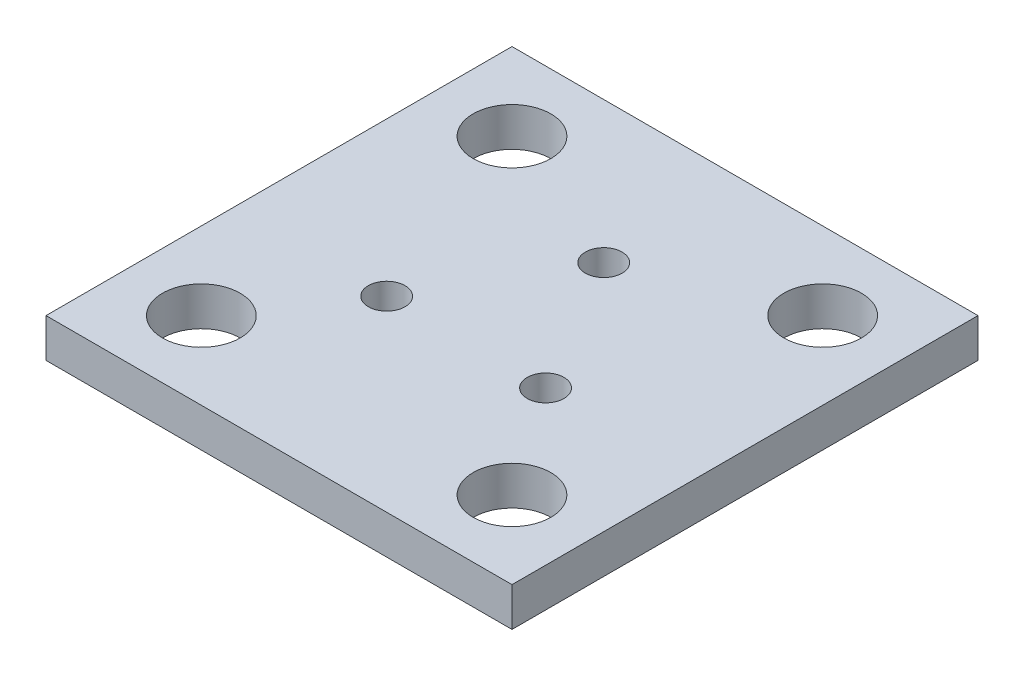
SolidWorks part; units mm, degrees
ref_plane "Front Plane" through (0, 0, 0) normal (0, 0, 1) x (1, 0, 0)
ref_plane "Top Plane" through (0, 0, 0) normal (0, 1, 0) x (1, 0, 0)
ref_plane "Right Plane" through (0, 0, 0) normal (1, 0, 0) x (0, 0, -1)
sketch "Sketch1" plane through (0, 0, 0) normal (0, 1, 0) x (1, 0, 0)
  line L1 (-19.05, -19.05) -> (19.05, -19.05)
  line L2 (-19.05, -19.05) -> (-19.05, 19.05)
  line L3 (-19.05, 19.05) -> (19.05, 19.05)
  line L4 (19.05, -19.05) -> (19.05, 19.05)
  line L5 (-19.05, -19.05) -> (19.05, 19.05) construction
  line L6 (-19.05, 19.05) -> (19.05, -19.05) construction
  circle A0 centre (0, 0) radius 19.05 construction
  dimension "D1" = 38.1
  dimension "D2" = 38.1
  dimension "D3" = 38.1
extrude "Boss-Extrude1" add sketch "Sketch1" along normal blind 3.175
sketch "Sketch2" plane through (0, 3.175, 0) normal (0, 1, 0) x (1, 0, 0)
  circle A0 centre (0, 0) radius 7.5 construction
  circle A1 centre (0, 7.5) radius 1.5
  circle A2 centre (6.4952, -3.75) radius 1.5
  circle A3 centre (-6.4952, -3.75) radius 1.5
  point P11 (0, 0)
  dimension "D2" = 15
  dimension "D3" = 3
  dimension "D1" = 3
extrude "Cut-Extrude1" cut sketch "Sketch2" against normal through all contours A1 | A3 | A2
sketch "Sketch3" plane through (0, 3.175, 0) normal (0, 1, 0) x (1, 0, 0)
  line L1 (-12.7, -12.7) -> (12.7, -12.7) construction
  line L2 (-12.7, -12.7) -> (-12.7, 12.7) construction
  line L3 (-12.7, 12.7) -> (12.7, 12.7) construction
  line L4 (12.7, -12.7) -> (12.7, 12.7) construction
  line L5 (-12.7, -12.7) -> (12.7, 12.7) construction
  line L6 (-12.7, 12.7) -> (12.7, -12.7) construction
  circle A0 centre (-12.7, 12.7) radius 3.175
  circle A1 centre (12.7, 12.7) radius 3.175
  circle A2 centre (12.7, -12.7) radius 3.175
  circle A3 centre (-12.7, -12.7) radius 3.175
  point P0 (0, 0)
  dimension "D3" = 6.35
  dimension "D1" = 25.4
  dimension "D2" = 25.4
  dimension "D4" = 2
  dimension "D5" = 2
extrude "Cut-Extrude2" cut sketch "Sketch3" against normal through all contours A0 | A3 | A2 | A1
equation "\"D3@Sketch1\"=\"D2@Sketch1\""
equation "\"D2@Sketch3\"=\"D1@Sketch3\""
